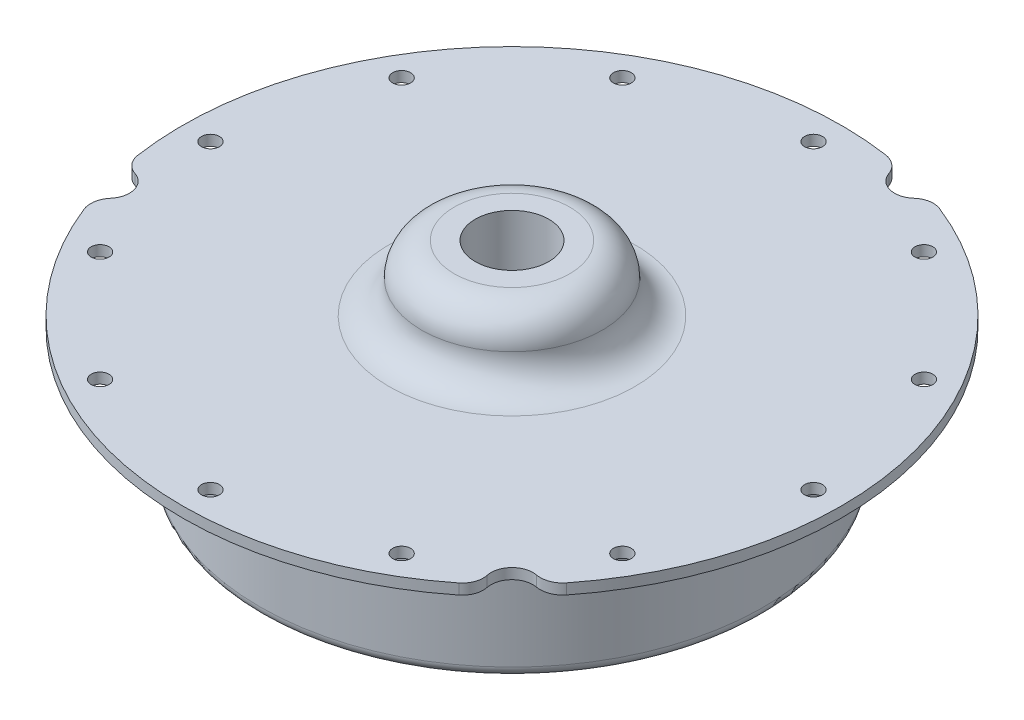
SolidWorks part; units mm, degrees
material "6063-T6"
ref_plane "Front Plane" through (0, 0, 0) normal (0, 0, 1) x (1, 0, 0)
ref_plane "Top Plane" through (0, 0, 0) normal (0, 1, 0) x (1, 0, 0)
ref_plane "Right Plane" through (0, 0, 0) normal (1, 0, 0) x (0, 0, -1)
ref_axis "Axis1" through (0, 55, 0) along (0, -1, 0)
sketch "Sketch1" plane through (0, 0, 0) normal (0, 0, 1) x (1, 0, 0)
  line L0 (-49.784, 0) -> (-39.6875, 0)
  line L1 (0, 55) -> (0, -55) construction
  line L2 (-49.784, 0) -> (-49.784, 1.5875)
  line L3 (-5.5562, 11.43) -> (-8.7312, 11.43)
  line L5 (-5.5562, 11.43) -> (-5.5562, 0)
  line L6 (-5.5562, 0) -> (0, 0) construction
  line L7 (-49.784, 0) -> (-49.784, 1.5875) construction
  line L8 (-5.5562, 1.5875) -> (-5.5562, 0) construction
  line L9 (-38.1, -1.5875) -> (-38.1, -17.4625)
  line L11 (-34.925, -17.4625) -> (-34.925, -3.175)
  line L12 (-31.75, 0) -> (-5.5562, 0)
  line L13 (0, -201000) -> (0, 249000) construction
  line L14 (-49.784, 1.5875) -> (-18.5737, 1.5875)
  arc A0 (-34.925, -3.175) -> (-31.75, 0) centre (-31.75, -3.175) cw
  arc A1 (-38.1, -1.5875) -> (-39.6875, 0) centre (-39.6875, -1.5875) ccw
  arc A2 (-18.5737, 1.5875) -> (-13.6525, 6.5088) centre (-18.5737, 6.5088) ccw
  arc A3 (-8.7312, 11.43) -> (-13.6525, 6.5088) centre (-8.7312, 6.5088) ccw
  arc A4 (-38.1, -17.4625) -> (-34.925, -17.4625) centre (-36.5125, -17.4625) ccw
  point P18 (-34.925, 0)
  dimension "D4" = 3.175
  dimension "D5" = 1.5875
  dimension "D1" = 3.175
  dimension "D2" = 38.1
  dimension "D3" = 17.4625
  dimension "D6" = 1.5875
  dimension "D7" = 3.175
  dimension "D8" = 11.43
revolve "Revolve1" add sketch "Sketch1" angle 360 about axis through (0, 55, 0) along (0, -1, 0)
ref_plane "Hole Location Plane" through (0, 3.175, 0) normal (0, 1, 0) x (1, 0, 0)
sketch "Hole Location" plane through (0, 3.175, 0) normal (0, 1, 0) x (1, 0, 0)
  line L0 (0, 0) -> (-45.5549, 0) construction
  circle A0 centre (0, 0) radius 45.5549 construction
  dimension "D1" = 91.1098
hole_wizard "#36 (0.1065) Diameter Hole1" positions "Sketch2" profile "Sketch3" hole size "#36" standard "ANSI Inch" end condition through all
sketch "Sketch2" plane through (0, 1.5875, 0) normal (0, 1, 0) x (1, 0, 0)
  point P0 (-45.5549, 0)
sketch "Sketch3" plane through (-45.5549, 1.5875, 0) normal (1, 0, 0) x (0, 0, 1)
  line L0 (0, 0) -> (0, 20.6375)
  line L1 (0, 20.6375) -> (1.3525, 20.6375)
  line L2 (1.3525, 20.6375) -> (1.3525, 0)
  line L5 (1.3525, 0) -> (0, 0)
  line L11 (0, -6.35) -> (0, 107.95) construction
  dimension "Thru Hole Dia." = 2.7051
  dimension "Thru Hole Depth" = 20.6375
pattern_circular "CirPattern1" count 12 over 360 about axis through (0, 0, 0) along (0, 1, 0) of "#36 (0.1065) Diameter Hole1"
hole_wizard "7/16 (0.4375) Diameter Hole1" positions "Sketch4" profile "Sketch5" hole size "7/16" standard "ANSI Inch" end condition through all
sketch "Sketch4" plane through (0, 11.43, 0) normal (0, 1, 0) x (1, 0, 0)
  point P0 (0, 0)
sketch "Sketch5" plane through (0, 11.43, 0) normal (1, 0, 0) x (0, 0, 1)
  line L0 (0, 0) -> (0, 30.48)
  line L1 (0, 30.48) -> (5.5562, 30.48)
  line L2 (5.5562, 30.48) -> (5.5562, 0)
  line L5 (5.5562, 0) -> (0, 0)
  line L11 (0, -6.35) -> (0, 107.95) construction
  dimension "Thru Hole Dia." = 11.1125
  dimension "Thru Hole Depth" = 30.48
sketch "Sketch6" plane through (0, 1.5875, 0) normal (0, 1, 0) x (1, 0, 0)
  line L0 (0, 0) -> (-48.0877, -12.885) construction
  line L1 (0, 0) -> (-45.5549, 0) construction
  circle A0 centre (0, 0) radius 49.784 construction
  arc A1 (-49.2429, -7.3202) -> (-47.095, -9.8692) centre (-46.1024, -6.8534) ccw
  arc A2 (-47.095, -9.8692) -> (-45.6723, -14.9458) centre (-48.0877, -12.885) cw
  circle A3 centre (0, 0) radius 49.784 construction
  arc A4 (-45.6723, -14.9458) -> (-46.2472, -18.4294) centre (-43.0722, -17.1641) ccw
  arc A5 (-46.2472, -18.4294) -> (-49.2429, -7.3202) centre (0, 0) cw
  arc A6 (9.8927, 47.0263) -> (7.1633, 49.2659) centre (6.6715, 45.8837) ccw
  arc A7 (15.0005, 45.7201) -> (9.8927, 47.0263) centre (12.885, 48.0877) cw
  arc A8 (18.282, 46.3057) -> (15.0005, 45.7201) centre (17.116, 43.3525) ccw
  arc A9 (7.1633, 49.2659) -> (18.282, 46.3057) centre (0, 0) cw
  arc A10 (35.7796, -32.0805) -> (39.0839, -30.8366) centre (36.4007, -28.7196) ccw
  arc A11 (32.0945, -35.8509) -> (35.7796, -32.0805) centre (35.2026, -35.2026) cw
  arc A12 (30.9609, -38.9855) -> (32.0945, -35.8509) centre (28.9864, -36.4992) ccw
  arc A13 (39.0839, -30.8366) -> (30.9609, -38.9855) centre (0, 0) cw
  point P31 (0, 0)
  dimension "D2" = 3.175
  dimension "D3" = 3.175
  dimension "D4" = 49.784
  dimension "D5" = 3.175
  dimension "D1" = 15
  dimension "D6" = 3
extrude "Cut-Extrude1" cut sketch "Sketch6" against normal up to surface (1.5875 mm away)
equation "\"D1@Hole Location\"=\"TANK DIAMETER@Cryo Tank.Assembly\"+\"GASKET SEAT THICKNESS@Cryo Tank.Assembly\"+\"LINER THICKNESS@Cryo Tank.Assembly\"+\"SHRINK FIT DELTA@Cryo Tank.Assembly\""
equation "\"D2@Sketch1\"=\"TANK DIAMETER@Cryo Tank.Assembly\"/2"
equation "\"D3@Sketch1\"=0.5+0.125+0.0625"
